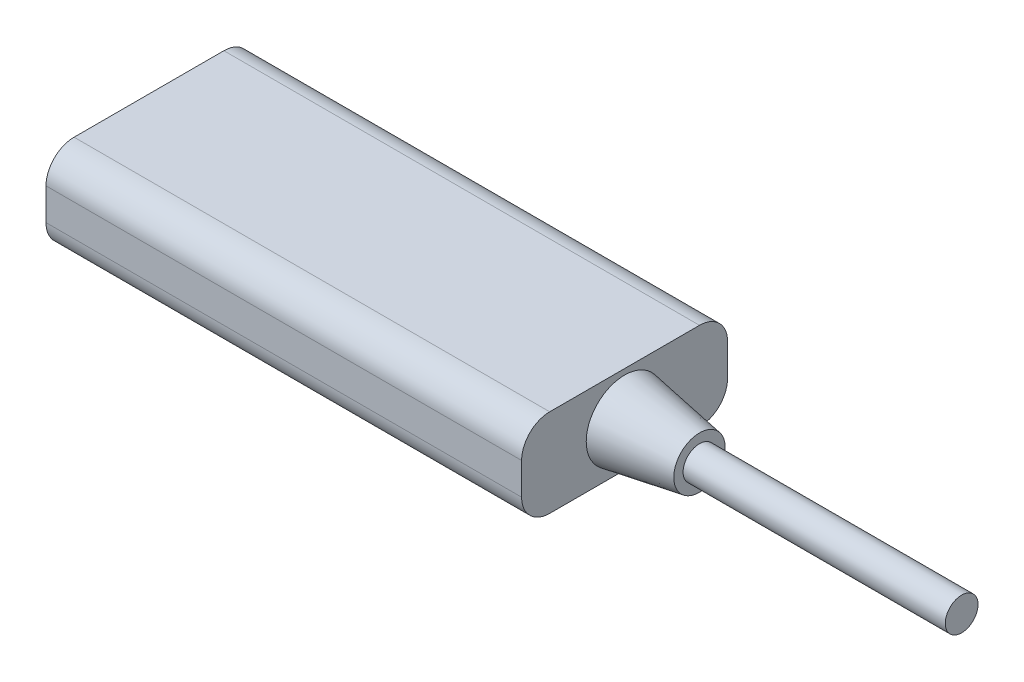
SolidWorks part; units mm, degrees
material "ABS"
ref_plane "Front" through (0, 0, 0) normal (0, 0, 1) x (1, 0, 0)
ref_plane "Top" through (0, 0, 0) normal (0, 1, 0) x (1, 0, 0)
ref_plane "Right" through (0, 0, 0) normal (1, 0, 0) x (0, 0, -1)
sketch "Эскиз1" plane through (0, 0, 0) normal (1, 0, 0) x (0, 0, -1)
  line L0 (11, -4.7) -> (11, 4.7)
  line L1 (11, -4.7) -> (-11, -4.7)
  line L2 (11, 4.7) -> (-11, 4.7)
  line L3 (-11, -4.7) -> (-11, 4.7)
  line L4 (11, -4.7) -> (-11, 4.7) construction
  line L5 (11, 4.7) -> (-11, -4.7) construction
  point P2 (0, 0)
  dimension "D1" = 9.4
  dimension "D2" = 22
extrude "Бобышка-Вытянуть1" add sketch "Эскиз1" against normal blind 50.8
sketch "Эскиз3" plane through (0, 0, 0) normal (0, 1, 0) x (1, 0, 0)
  line L0 (0, 0) -> (36, 0)
  line L1 (36, 0) -> (36, 1.75)
  line L2 (36, 1.75) -> (8, 1.75)
  line L3 (8, 1.75) -> (8, 2.75)
  line L4 (8, 2.75) -> (0, 4.1)
  line L5 (0, 11) -> (0, -11) construction
  line L6 (0, 4.1) -> (0, 0)
  dimension "D1" = 4.1
  dimension "D2" = 36
  dimension "D3" = 1.75
  dimension "D4" = 2.75
  dimension "D5" = 8
revolve "Повернуть1" add sketch "Эскиз3" angle 360 about L0
fillet "Скругление1" radius 3 4 edges at (-25.4, -4.7, -11) (-25.4, 4.7, -11) (-25.4, -4.7, 11) (-25.4, 4.7, 11)
sketch "Эскиз4" plane through (-50.8, 0, 0) normal (-1, 0, 0) x (0, 0, 1)
  line L0 (0, -4.7) -> (0, 0.6) construction
  line L1 (8, -4.7) -> (-8, -4.7) construction
  line L2 (0, 0.6) -> (4.4, 0.6) construction
  line L3 (0, 0.6) -> (-4.4, 0.6) construction
  circle A0 centre (-4.4, 0.6) radius 1.65
  circle A1 centre (4.4, 0.6) radius 1.65
  dimension "D4" = 3.3
  dimension "D5" = 3.3
  dimension "D1" = 5.3
  dimension "D2" = 4.4
  dimension "D3" = 4.4
extrude "Вырез-Вытянуть1" cut sketch "Эскиз4" against normal blind 10
